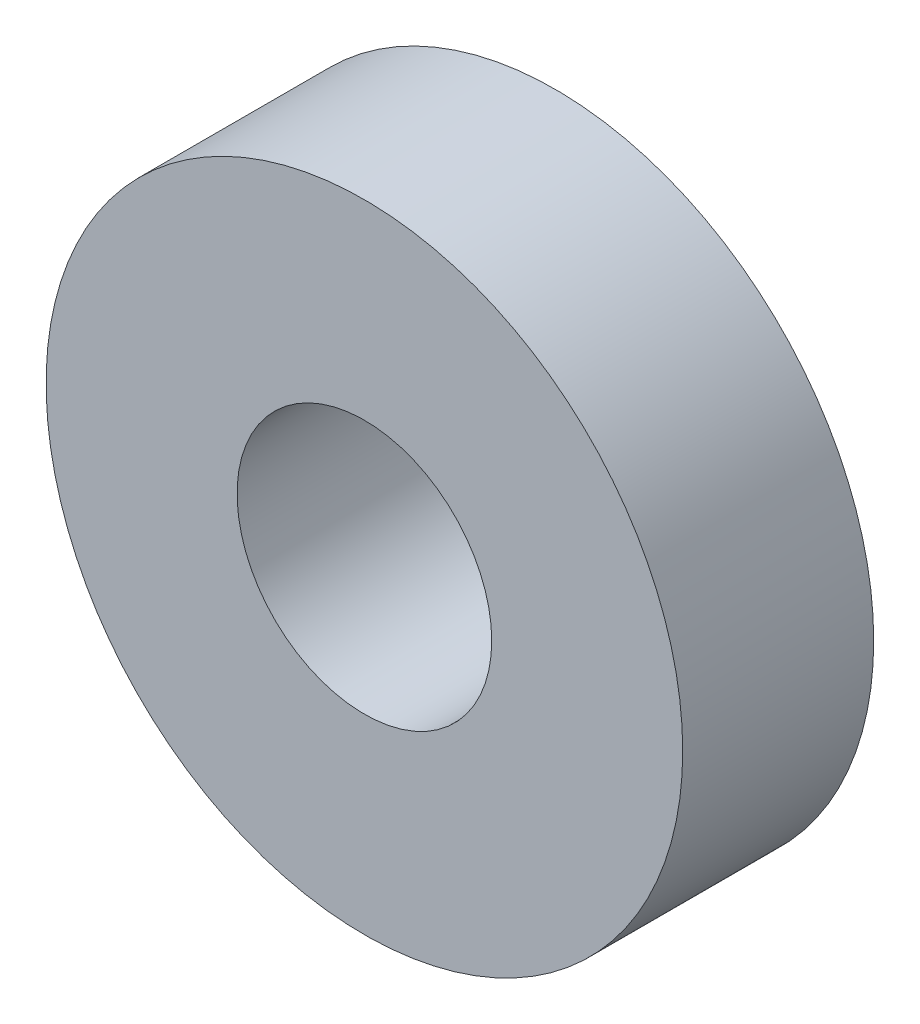
SolidWorks part; units mm, degrees
material "Stainless Steel (ferritic)"
ref_plane "Front Plane" through (0, 0, 0) normal (0, 0, 1) x (1, 0, 0)
ref_plane "Top Plane" through (0, 0, 0) normal (0, 1, 0) x (1, 0, 0)
ref_plane "Right Plane" through (0, 0, 0) normal (1, 0, 0) x (0, 0, -1)
sketch "Sketch1" plane through (0, 0, 0) normal (0, 0, 1) x (1, 0, 0)
  circle A0 centre (0, 0) radius 10
  circle A1 centre (0, 0) radius 4
  dimension "D1" = 20
  dimension "D2" = 8
extrude "Boss-Extrude1" add sketch "Sketch1" along normal blind 6
